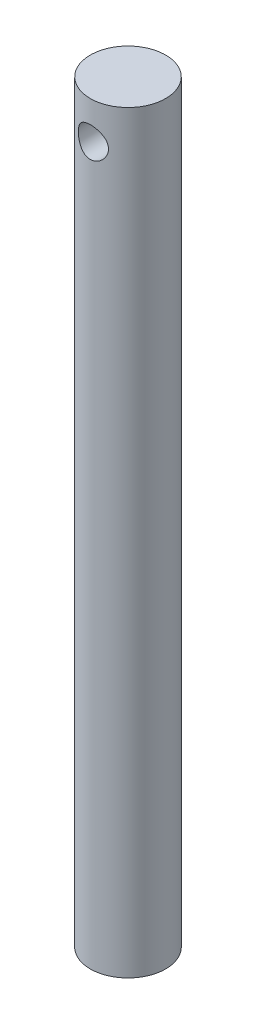
SolidWorks part; units mm, degrees
material "ABS"
ref_plane "Front Plane" through (0, 0, 0) normal (0, 0, 1) x (1, 0, 0)
ref_plane "Top Plane" through (0, 0, 0) normal (0, 1, 0) x (1, 0, 0)
ref_plane "Right Plane" through (0, 0, 0) normal (1, 0, 0) x (0, 0, -1)
sketch "Sketch1" plane through (0, 0, 0) normal (0, 1, 0) x (1, 0, 0)
  circle A0 centre (0, 0) radius 15
  dimension "D1" = 30
extrude "Boss-Extrude1" add sketch "Sketch1" along normal blind 300
sketch "Sketch2" plane through (0, 0, 0) normal (0, 0, 1) x (1, 0, 0)
  line L0 (15, 300) -> (-15, 300) construction
  circle A0 centre (0, 285) radius 6
  dimension "D2" = 12
  dimension "D1" = 15
extrude "Cut-Extrude1" cut sketch "Sketch2" along normal through all both and the other way through all
sketch "Sketch3" plane through (0, 0, 0) normal (0, -1, 0) x (1, 0, 0)
  circle A0 centre (0, 0) radius 4
  dimension "D1" = 8
extrude "Cut-Extrude2" cut sketch "Sketch3" against normal blind 2.85
sketch "Sketch4" plane through (0, 2.85, 0) normal (0, -1, 0) x (1, 0, 0)
  circle A0 centre (0, 0) radius 2.25
  dimension "D1" = 4.5
extrude "Cut-Extrude3" cut sketch "Sketch4" against normal blind 2.5
sketch "Sketch5" plane through (0, 0, 0) normal (1, 0, 0) x (0, 0, -1)
  line L0 (-15, 0) -> (15, 0) construction
  line L1 (0, 20) -> (-10, 20)
  line L2 (0, 20) -> (0, 270)
  line L3 (0, 270) -> (-10, 270)
  line L4 (-10, 20) -> (-10, 270)
  dimension "D1" = 250
  dimension "D2" = 10
  dimension "D3" = 20
revolve "Cut-Revolve1" [suppressed] cut sketch "Sketch5" angle 360 about L2
